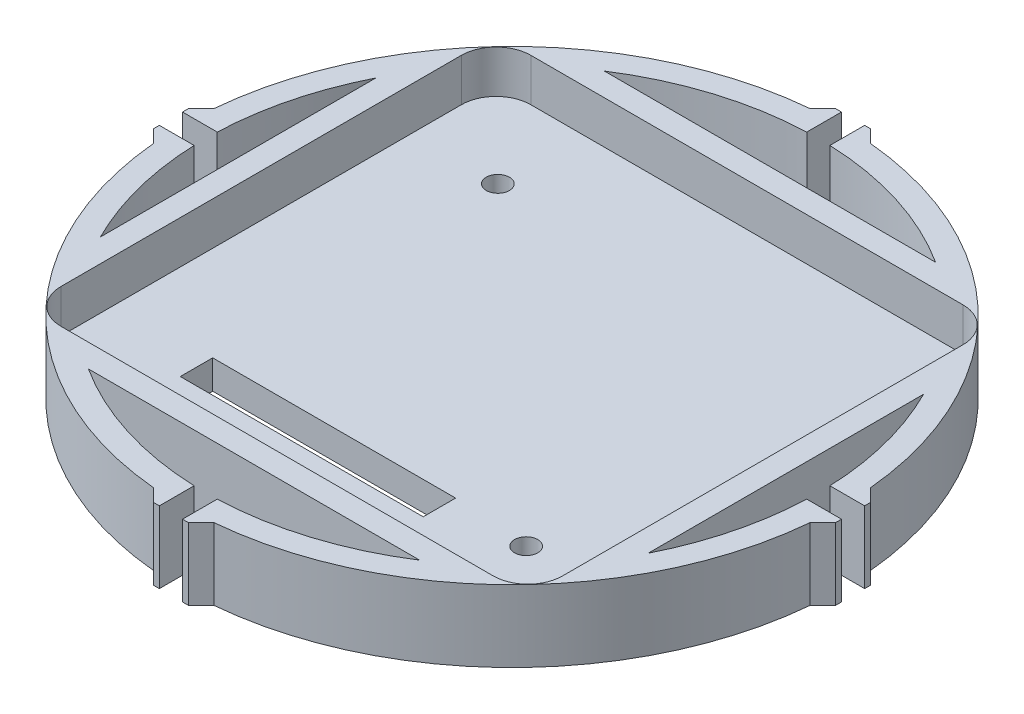
SolidWorks part; units mm, degrees
ref_plane "Front Plane" through (0, 0, 0) normal (0, 0, 1) x (1, 0, 0)
ref_plane "Top Plane" through (0, 0, 0) normal (0, 1, 0) x (1, 0, 0)
ref_plane "Right Plane" through (0, 0, 0) normal (1, 0, 0) x (0, 0, -1)
sketch "Sketch1" plane through (0, 0, 0) normal (0, 1, 0) x (1, 0, 0)
  circle A0 centre (0, 0) radius 28.5
  dimension "D1" = 57
extrude "Boss-Extrude1" add sketch "Sketch1" along normal blind 6.2
sketch "Sketch2" plane through (0, 6.2, 0) normal (0, 1, 0) x (1, 0, 0)
  line L0 (0, 28.5) -> (0, -28.5) construction
  line L1 (-21.675, 20.3) -> (21.675, 20.3)
  line L2 (-21.675, 20.3) -> (-21.675, -20.3)
  line L3 (-21.675, -20.3) -> (21.675, -20.3)
  line L4 (21.675, 20.3) -> (21.675, -20.3)
  line L5 (-21.675, 20.3) -> (21.675, -20.3) construction
  line L6 (-21.675, -20.3) -> (21.675, 20.3) construction
  line L7 (-28.5, 0) -> (28.5, 0) construction
  circle A0 centre (-18.675, 17.3) radius 3
  circle A1 centre (0, 0) radius 28.5 construction
  circle A2 centre (18.675, 17.3) radius 3
  circle A3 centre (18.675, -17.3) radius 3
  circle A4 centre (-18.675, -17.3) radius 3
  point P0 (0, 0)
  dimension "D3" = 6
  dimension "D1" = 43.35
  dimension "D2" = 40.6
extrude "Cut-Extrude1" cut sketch "Sketch2" against normal blind 3.7 contours L2 A4 L3 A3 L4 A2 L1 A0 | A0 | A2 | A3 | A4
sketch "Sketch3" plane through (0, 2.5, 0) normal (0, 1, 0) x (1, 0, 0)
  line L0 (-21.675, -13.8) -> (21.675, -13.8) construction
  line L1 (-21.675, 17.3) -> (-21.675, -17.3) construction
  line L2 (21.675, 17.3) -> (21.675, -17.3) construction
  line L3 (-21.675, 17.3) -> (-21.675, -17.3) construction
  line L4 (-13.475, -12.4) -> (7.525, -12.4)
  line L5 (-13.475, -12.4) -> (-13.475, -15.2)
  line L6 (-13.475, -15.2) -> (7.525, -15.2)
  line L7 (7.525, -12.4) -> (7.525, -15.2)
  line L8 (-13.475, -12.4) -> (7.525, -15.2) construction
  line L9 (-13.475, -15.2) -> (7.525, -12.4) construction
  line L10 (-18.675, -20.3) -> (18.675, -20.3) construction
  line L11 (-18.675, 20.3) -> (18.675, 20.3) construction
  line L12 (-28.5, 0) -> (28.5, 0) construction
  line L13 (0, 28.5) -> (0, -28.5) construction
  line L14 (0, 0) -> (19.2228, 21.0412) construction
  line L15 (-14.175, 12.95) -> (0, 0) construction
  circle A0 centre (-14.175, 12.95) radius 1
  circle A1 centre (0, 0) radius 28.5 construction
  circle A2 centre (14.175, -12.95) radius 1
  point P6 (-2.975, -13.8)
  dimension "D5" = 2
  dimension "D1" = 8.2
  dimension "D2" = 21
  dimension "D3" = 2.8
  dimension "D4" = 5.1
  dimension "D6" = 7.5
  dimension "D7" = 7.35
extrude "Cut-Extrude2" cut sketch "Sketch3" against normal up to next contours A0 | L7 L4 L5 L6 | A2
sketch "Sketch4" plane through (0, 6.2, 0) normal (0, 1, 0) x (1, 0, 0)
  line L0 (0, 20.3) -> (0, 22.3) construction
  line L1 (-28.5, 1) -> (28.5, 1)
  line L2 (-28.5, 1) -> (-28.5, -1)
  line L3 (-28.5, -1) -> (28.5, -1)
  line L4 (28.5, 1) -> (28.5, -1)
  line L5 (-28.5, 1) -> (28.5, -1) construction
  line L6 (-28.5, -1) -> (28.5, 1) construction
  line L7 (-1, -28.5) -> (1, -28.5)
  line L8 (-1, -28.5) -> (-1, 28.5)
  line L9 (-1, 28.5) -> (1, 28.5)
  line L10 (1, -28.5) -> (1, 28.5)
  line L11 (-1, -28.5) -> (1, 28.5) construction
  line L12 (-1, 28.5) -> (1, -28.5) construction
  line L13 (23.675, -22.3) -> (-23.675, -22.3)
  line L14 (23.675, -22.3) -> (23.675, 22.3)
  line L15 (23.675, 22.3) -> (-23.675, 22.3)
  line L16 (-23.675, -22.3) -> (-23.675, 22.3)
  line L17 (23.675, -22.3) -> (-23.675, 22.3) construction
  line L18 (23.675, 22.3) -> (-23.675, -22.3) construction
  line L19 (-18.675, 20.3) -> (18.675, 20.3) construction
  line L20 (-23.675, 0) -> (-21.675, 0) construction
  line L21 (-21.675, 17.3) -> (-21.675, -17.3) construction
  line L22 (-26.5, 0) -> (-28.5, 0) construction
  circle A0 centre (0, 0) radius 28.5 construction
  circle A1 centre (0, 0) radius 26.5
  point P0 (0, 0)
  circle M6 centre (0, 0) radius 28.5
  dimension "D1" = 2
extrude "Cut-Extrude3" cut sketch "Sketch4" against normal up to next contours L8 A1 L15 | L15 A1 L10 | A1 L10 L8 M6 | L10 A1 L8 L15 | A1 L1 L3 M6 | L1 A1 L3 L16 | L16 A1 L1 | L3 A1 L16 | L13 A1 L8 | L10 A1 L13 | L8 A1 L10 L13 | A1 L8 L10 M6 | L1 A1 L14 | L14 A1 L3 | L3 A1 L1 L14 | A1 L3 L1 M6
sketch "Sketch5" plane through (0, 6.2, 0) normal (0, 1, 0) x (1, 0, 0)
  line L0 (-1, 28.4825) -> (-1, 29.4825)
  line L1 (-1, 29.4825) -> (-1.5, 29.4825)
  line L2 (-1.5, 29.4825) -> (-2.6014, 28.381)
  line L3 (0, 28.5) -> (0, -28.5) construction
  line L4 (-28.5, 0) -> (28.5, 0) construction
  line L5 (-20.1525, -20.1525) -> (20.1525, 20.1525) construction
  line L6 (1, 28.4825) -> (1, 29.4825)
  line L7 (1, 29.4825) -> (1.5, 29.4825)
  line L8 (1.5, 29.4825) -> (2.6014, 28.381)
  line L9 (1.5, -29.4825) -> (2.6014, -28.381)
  line L10 (1, -29.4825) -> (1.5, -29.4825)
  line L11 (1, -28.4825) -> (1, -29.4825)
  line L12 (-1, -28.4825) -> (-1, -29.4825)
  line L13 (-1, -29.4825) -> (-1.5, -29.4825)
  line L14 (-1.5, -29.4825) -> (-2.6014, -28.381)
  line L15 (29.4825, 1.5) -> (28.381, 2.6014)
  line L16 (29.4825, 1) -> (29.4825, 1.5)
  line L17 (28.4825, 1) -> (29.4825, 1)
  line L18 (29.4825, -1) -> (29.4825, -1.5)
  line L19 (28.4825, -1) -> (29.4825, -1)
  line L20 (29.4825, -1.5) -> (28.381, -2.6014)
  line L21 (-29.4825, 1.5) -> (-28.381, 2.6014)
  line L22 (-29.4825, 1) -> (-29.4825, 1.5)
  line L23 (-28.4825, 1) -> (-29.4825, 1)
  line L24 (-29.4825, -1.5) -> (-28.381, -2.6014)
  line L25 (-29.4825, -1) -> (-29.4825, -1.5)
  line L26 (-28.4825, -1) -> (-29.4825, -1)
  arc A1 (-1, 28.4825) -> (-28.4825, 1) centre (0, 0) ccw construction
  circle A2 centre (0, 0) radius 28.5
  arc M5 (-28.4825, -1) -> (-1, -28.4825) centre (0, 0) ccw
  arc M11 (1, -28.4825) -> (28.4825, -1) centre (0, 0) ccw
  arc M17 (28.4825, 1) -> (1, 28.4825) centre (0, 0) ccw
  arc M23 (-1, 28.4825) -> (-28.4825, 1) centre (0, 0) ccw
  dimension "D1" = 0.5
  dimension "D2" = 1
  dimension "D3" = 135
  dimension "D4" = 45
extrude "Boss-Extrude2" add sketch "Sketch5" against normal up to surface (6.2 mm away) contours L1 L2 L0 M23 | L8 L7 L6 M17 | L17 L16 L15 M17 | L20 L18 L19 M11 | L26 L25 L24 M5 | L23 L21 L22 M23 | L14 L13 L12 M5 | L11 L10 L9 M11 up to face at (-2.975, 0, 13.8)
